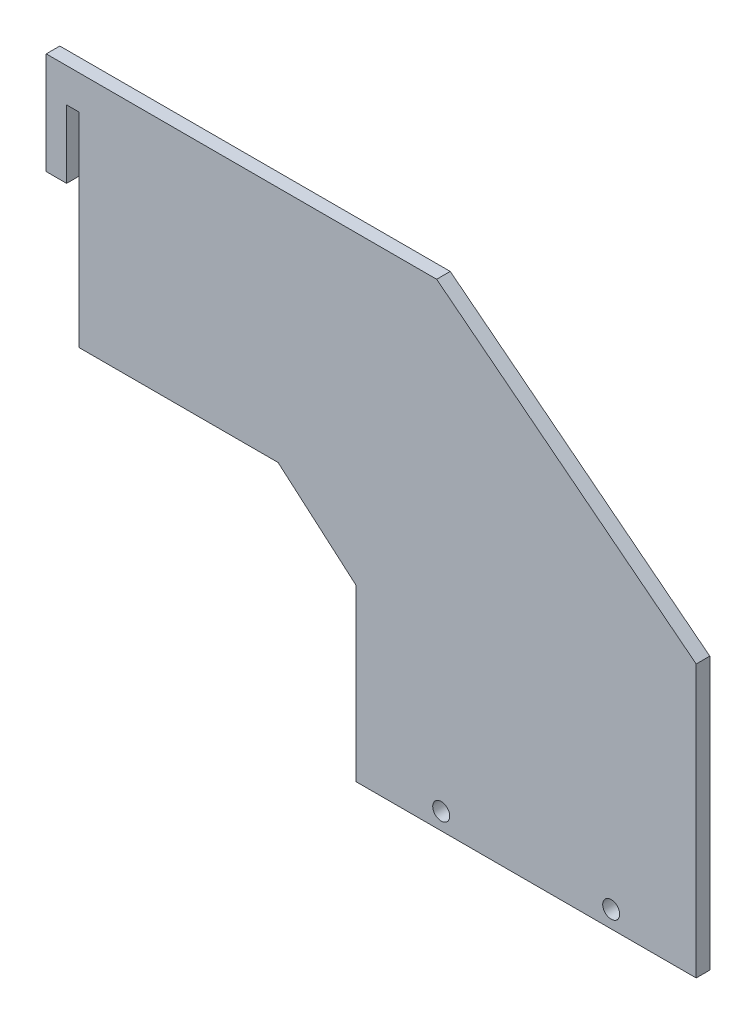
SolidWorks part; units mm, degrees
ref_plane "Спереди" through (0, 0, 0) normal (0, 0, 1) x (1, 0, 0)
ref_plane "Сверху" through (0, 0, 0) normal (0, 1, 0) x (1, 0, 0)
ref_plane "Справа" through (0, 0, 0) normal (1, 0, 0) x (0, 0, -1)
sketch "Эскиз1" plane through (0, 0, 0) normal (0, 0, 1) x (1, 0, 0)
  line L1 (87.1938, -36.8506) -> (87.1938, -86.8506)
  line L2 (5.7114, 43.0018) -> (5.7114, -16.9982)
  line L4 (110.85, 53.0018) -> (187.1938, -6.8286)
  line L5 (87.1938, -86.8506) -> (187.1938, -86.8286)
  line L6 (5.7114, -16.9982) -> (64.2083, -16.9982)
  line L7 (64.2083, -16.9982) -> (87.1938, -36.8506)
  line L15 (187.1938, -86.8286) -> (187.1938, -6.8286)
  line L18 (110.85, 53.0018) -> (6, 53.0018)
  line L19 (6, 53.0018) -> (-4, 53.0018)
  line L20 (-4, 53.0018) -> (-4, 23.0018)
  line L22 (-4, 23.0018) -> (2, 23.0018)
  line L24 (2, 23.0018) -> (2, 43.0018)
  line L25 (2, 43.0018) -> (5.7114, 43.0018)
  dimension "D2" = 60
  dimension "D1" = 100
  dimension "D8" = 10
  dimension "D9" = 30
extrude "Бобышка-Вытянуть1" add sketch "Эскиз1" along normal blind 4
sketch "Эскиз2" plane through (0, 0, 4) normal (0, 0, 1) x (1, 0, 0)
  line L0 (87.1949, -56.0275) -> (137.1949, -56.0275) construction
  line L1 (137.1949, -56.0275) -> (187.1949, -56.0275) construction
  line L2 (80.17, -86.8506) -> (80.17, -81.8506) construction
  circle A0 centre (112.1949, -81.8506) radius 2.5
  circle A1 centre (162.1949, -81.8506) radius 2.5
  dimension "D4" = 5
  dimension "D5" = 5
  dimension "D1" = 50
  dimension "D2" = 50
  dimension "D3" = 5
extrude "Вырез-Вытянуть1" cut sketch "Эскиз2" against normal through all
